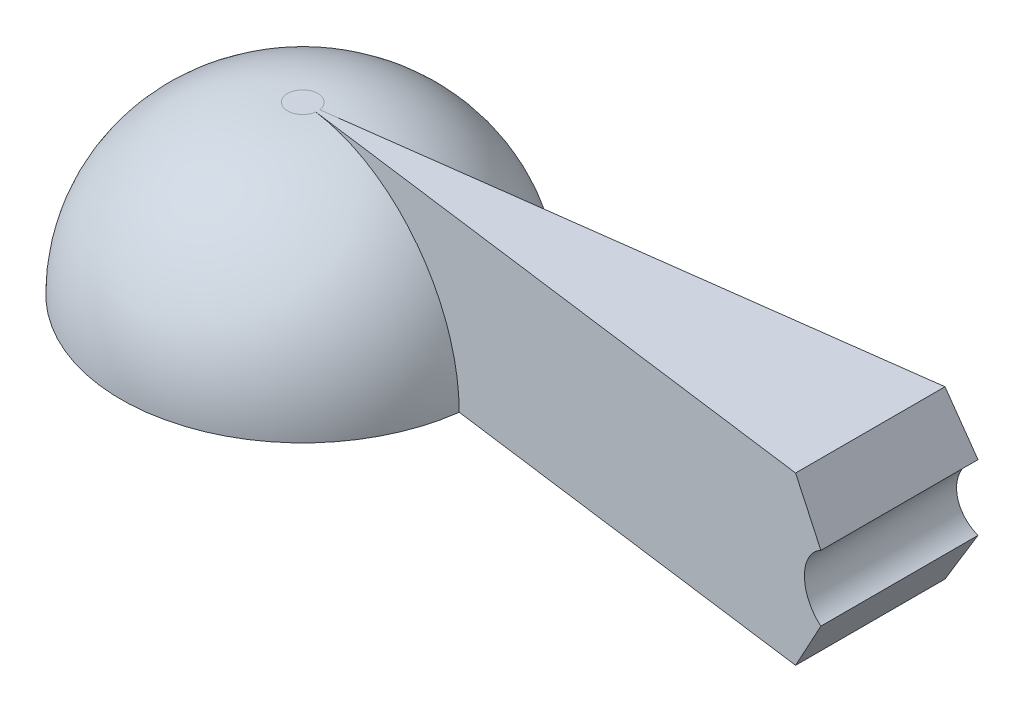
SolidWorks part; units mm, degrees
material "ABS"
ref_plane "Front Plane" through (0, 0, 0) normal (0, 0, 1) x (1, 0, 0)
ref_plane "Top Plane" through (0, 0, 0) normal (0, 1, 0) x (1, 0, 0)
ref_plane "Right Plane" through (0, 0, 0) normal (1, 0, 0) x (0, 0, -1)
sketch "Sketch1" plane through (0, 0, 0) normal (0, 0, 1) x (1, 0, 0)
  line L0 (0, 12.7) -> (-1.27, 12.7)
  line L1 (12.7, 0) -> (13.97, 0)
  line L2 (0, 13.97) -> (-1.27, 13.97)
  line L3 (-1.27, 13.97) -> (-1.27, 0) construction
  line L4 (-1.27, 12.7) -> (-1.27, 13.97)
  arc A0 (12.7, 0) -> (0, 12.7) centre (0, 0) ccw
  arc A1 (13.97, 0) -> (0, 13.97) centre (0, 0) ccw
  dimension "D1" = 12.7
  dimension "D3" = 1.27
  dimension "D4" = 1.27
  dimension "D2" = 1.27
revolve "Revolve1" add sketch "Sketch1" angle 360 about L3
sketch "Sketch3" plane through (0, 0, 0) normal (0, 0, 1) x (1, 0, 0)
  line L0 (0, 13.97) -> (50.8, 13.97)
  line L2 (13.97, 0) -> (50.8, 0)
  line L3 (50.8, 0) -> (50.8, 13.97)
  line L4 (-1.27, 13.97) -> (-1.27, 0) construction
  line L5 (0, 13.97) -> (-2.54, 13.97) construction
  arc A0 (13.97, 0) -> (0, 13.97) centre (0, 0) ccw
  dimension "D1" = 50.8
revolve "Revolve2" add sketch "Sketch3" angle 7.5 about L4 other way angle 7.5
sketch "Sketch4" plane through (0, 0, 0) normal (0, 0, 1) x (1, 0, 0)
  line L0 (50.3545, 6.985) -> (46.3217, 0) construction
  line L1 (50.3545, 0) -> (50.3545, 13.97) construction
  line L2 (50.3545, 13.97) -> (57.4469, 13.97)
  line L3 (57.4469, 13.97) -> (57.4469, -0.5116)
  line L4 (57.4469, -0.5116) -> (50.3545, 0)
  line L5 (13.8396, 0) -> (50.3545, 0) construction
  line L6 (46.3217, 13.97) -> (50.3545, 13.97) construction
  line L7 (50.3545, 0) -> (50.3545, 13.97) construction
  line L8 (48.767, 9.7346) -> (46.3217, 13.97)
  line L9 (50.3545, 6.985) -> (46.3217, 6.985) construction
  line L10 (50.3545, 6.985) -> (46.3217, 13.97) construction
  line L11 (50.3545, 13.97) -> (-0.0109, 13.97) construction
  line L12 (46.3217, 0) -> (46.3217, 13.97) construction
  line L13 (46.3217, 13.97) -> (50.3545, 13.97)
  line L14 (50.3545, 0) -> (46.3217, 0)
  line L15 (46.3217, 0) -> (48.767, 4.2354)
  arc A0 (48.767, 9.7346) -> (48.767, 4.2354) centre (50.3545, 6.985) ccw
  dimension "D1" = 120
  dimension "D2" = 3.175
extrude "Cut-Extrude1" cut sketch "Sketch4" against normal through all and the other way through all
